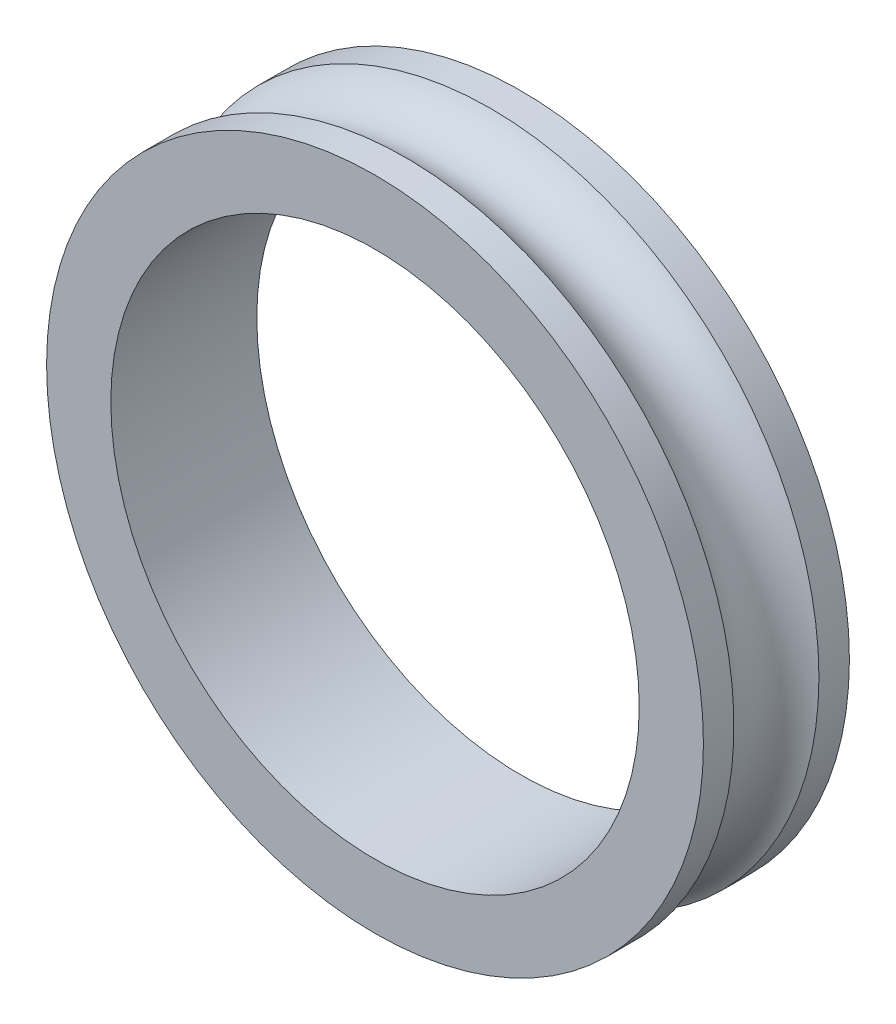
SolidWorks part; units mm, degrees
material "Nylon 101 50%"
ref_plane "Front Plane" through (0, 0, 0) normal (0, 0, 1) x (1, 0, 0)
ref_plane "Top Plane" through (0, 0, 0) normal (0, 1, 0) x (1, 0, 0)
ref_plane "Right Plane" through (0, 0, 0) normal (1, 0, 0) x (0, 0, -1)
ref_axis "Axis1" through (0, 0, -18.4628) along (0, 0, 1)
sketch "Sketch1" plane through (0, 0, 0) normal (0, 0, 1) x (1, 0, 0)
  line L1 (18.1, 0) -> (24, 0) construction
  line L2 (24, 0) -> (29.9, 0) construction
  line L4 (0, 22.5) -> (0, 24) construction
  circle A1 centre (0, 0) radius 24 construction
  circle A4 centre (0, 0) radius 29.9 construction
  circle A5 centre (0, 0) radius 29.9 construction
  circle A6 centre (0, 0) radius 18.1 construction
  circle A7 centre (0, 0) radius 18.1 construction
  circle A8 centre (0, 0) radius 22.5
  dimension "D1" = 1.5
extrude "Boss-Extrude1" add sketch "Sketch1" along normal up to surface (10 mm away)
sketch "Sketch2" plane through (0, 0, 10) normal (0, 0, 1) x (1, 0, 0)
  circle A3 centre (0, 0) radius 18.1 construction
  circle A4 centre (0, 0) radius 18.1 construction
  circle A5 centre (0, 0) radius 18.1
extrude "Cut-Extrude1" cut sketch "Sketch2" against normal up to next
sketch "Sketch3" plane through (0, 0, 0) normal (0, 1, 0) x (1, 0, 0)
  line L0 (-20.825, -5) -> (-20.725, -5) construction
  circle A0 centre (-24, -5) radius 3.175 construction
  circle A1 centre (-24, -5) radius 3.175 construction
  circle A2 centre (-24, -5) radius 3.275
  dimension "D1" = 0.1
revolve "Cut-Revolve1" cut sketch "Sketch3" angle 360 about axis through (0, 0, -18.4628) along (0, 0, 1)
equation "\"10.00mmf\"=10"
